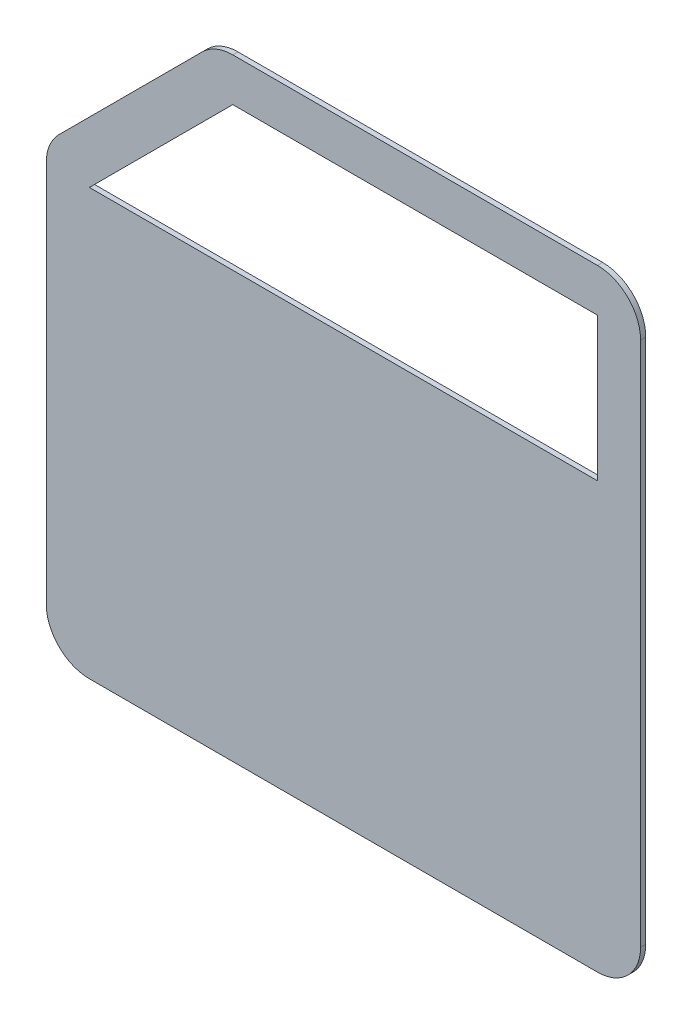
SolidWorks part; units mm, degrees
material "AISI 316 Stainless Steel Sheet (SS)"
ref_plane "Front Plane" through (0, 0, 0) normal (0, 0, 1) x (1, 0, 0)
ref_plane "Top Plane" through (0, 0, 0) normal (0, 1, 0) x (1, 0, 0)
ref_plane "Right Plane" through (0, 0, 0) normal (1, 0, 0) x (0, 0, -1)
sketch "Sketch1" plane through (0, 0, 0) normal (0, 0, 1) x (1, 0, 0)
  line L0 (481.9797, 377.6777) -> (398.7889, 294.4868) construction
  line L1 (711.1767, 385) -> (499.6574, 385) construction
  line L2 (736.1767, 55) -> (736.1767, 360) construction
  line L3 (416.4665, 30) -> (711.1767, 30) construction
  line L4 (391.4665, 276.8092) -> (391.4665, 55) construction
  line L5 (711.1767, 385) -> (499.6574, 385)
  line L6 (736.1767, 55) -> (736.1767, 360)
  line L7 (416.4665, 30) -> (711.1767, 30)
  line L8 (481.9797, 377.6777) -> (398.7889, 294.4868)
  line L9 (391.4665, 276.8092) -> (391.4665, 55)
  line L10 (416.4665, 276.8092) -> (499.6574, 360)
  line L11 (499.6574, 360) -> (711.1767, 360)
  line L12 (711.1767, 360) -> (711.1767, 276.8092)
  line L13 (711.1767, 276.8092) -> (416.4665, 276.8092)
  arc A0 (711.1767, 30) -> (736.1767, 55) centre (711.1767, 55) ccw construction
  arc A1 (499.6574, 385) -> (481.9797, 377.6777) centre (499.6574, 360) ccw construction
  arc A2 (736.1767, 360) -> (711.1767, 385) centre (711.1767, 360) ccw construction
  arc A3 (398.7889, 294.4868) -> (391.4665, 276.8092) centre (416.4665, 276.8092) ccw construction
  arc A4 (391.4665, 55) -> (416.4665, 30) centre (416.4665, 55) ccw construction
  arc A5 (499.6574, 385) -> (481.9797, 377.6777) centre (499.6574, 360) ccw
  arc A6 (736.1767, 360) -> (711.1767, 385) centre (711.1767, 360) ccw
  arc A7 (711.1767, 30) -> (736.1767, 55) centre (711.1767, 55) ccw
  arc A8 (398.7889, 294.4868) -> (391.4665, 276.8092) centre (416.4665, 276.8092) ccw
  arc A9 (391.4665, 55) -> (416.4665, 30) centre (416.4665, 55) ccw
extrude "Boss-Extrude1" add sketch "Sketch1" against normal blind 3
